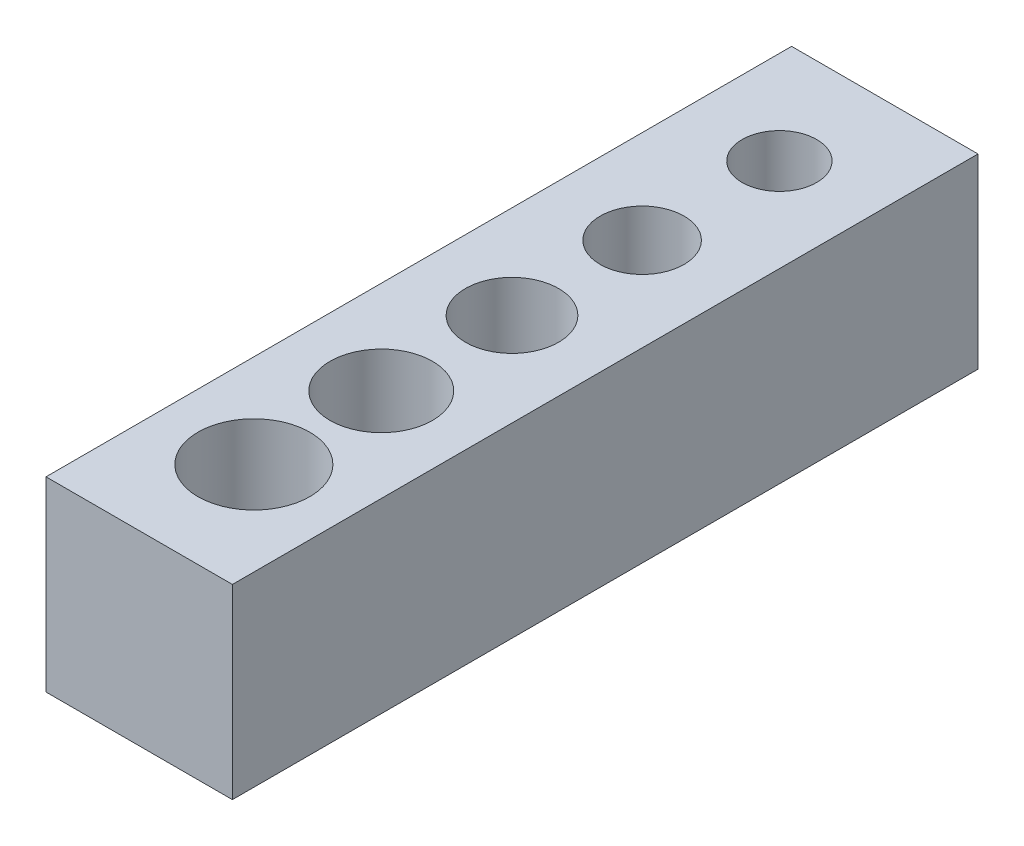
SolidWorks part; units mm, degrees
ref_plane "Front Plane" through (0, 0, 0) normal (0, 0, 1) x (1, 0, 0)
ref_plane "Top Plane" through (0, 0, 0) normal (0, 1, 0) x (1, 0, 0)
ref_plane "Right Plane" through (0, 0, 0) normal (1, 0, 0) x (0, 0, -1)
sketch "Sketch1" plane through (0, 0, 0) normal (0, 1, 0) x (1, 0, 0)
  line L1 (-5, -20) -> (5, -20)
  line L2 (-5, -20) -> (-5, 20)
  line L3 (-5, 20) -> (5, 20)
  line L4 (5, -20) -> (5, 20)
  line L5 (-5, -20) -> (5, 20) construction
  line L6 (-5, 20) -> (5, -20) construction
  circle A0 centre (0, 0) radius 2.5
  circle A1 centre (0, 6.9811) radius 2.25
  circle A2 centre (0, -7.0139) radius 2.75
  circle A3 centre (0, 14.3454) radius 2
  circle A4 centre (0, -13.8488) radius 3
  point P0 (0, 0)
  point P16 (-53.8192, 19.1114)
  dimension "D1" = 5
  dimension "D4" = 4.5
  dimension "D5" = 5.5
  dimension "D6" = 4
  dimension "D7" = 6
  dimension "D2" = 10
  dimension "D3" = 40
extrude "Boss-Extrude1" add sketch "Sketch1" along normal blind 10
